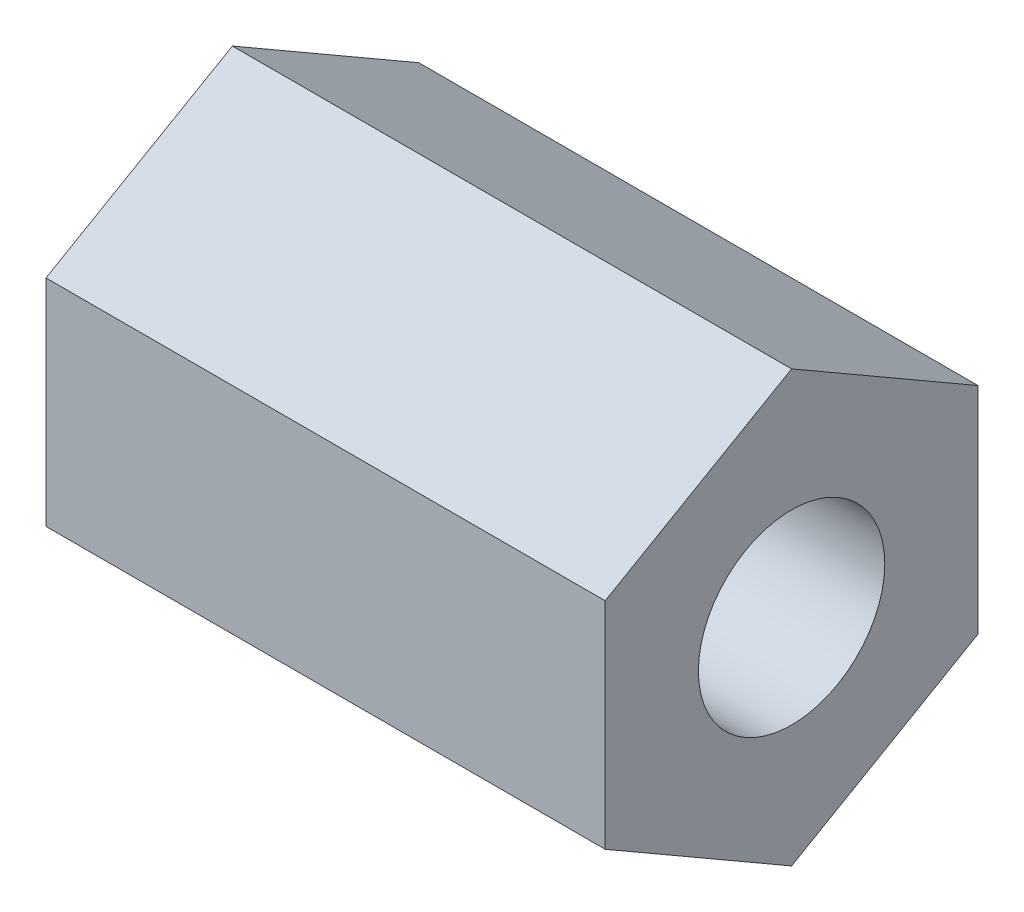
SolidWorks part; units mm, degrees
material "6061-T6 (SS)"
ref_plane "Front Plane" through (0, 0, 0) normal (0, 0, 1) x (1, 0, 0)
ref_plane "Top Plane" through (0, 0, 0) normal (0, 1, 0) x (1, 0, 0)
ref_plane "Right Plane" through (0, 0, 0) normal (1, 0, 0) x (0, 0, -1)
sketch "Sketch1" plane through (0, 0, 0) normal (1, 0, 0) x (0, 0, -1)
  line L1 (0, 7.3323) -> (-6.35, 3.6662)
  line L2 (-6.35, 3.6662) -> (-6.35, -3.6662)
  line L3 (-6.35, -3.6662) -> (0, -7.3323)
  line L4 (0, -7.3323) -> (6.35, -3.6662)
  line L5 (6.35, -3.6662) -> (6.35, 3.6662)
  line L6 (6.35, 3.6662) -> (0, 7.3323)
  circle A0 centre (0, 0) radius 6.35 construction
  circle A1 centre (0, 0) radius 3.175
  dimension "D1" = 12.7
  dimension "D2" = 6.35
extrude "Boss-Extrude1" add sketch "Sketch1" along normal blind 19.05
